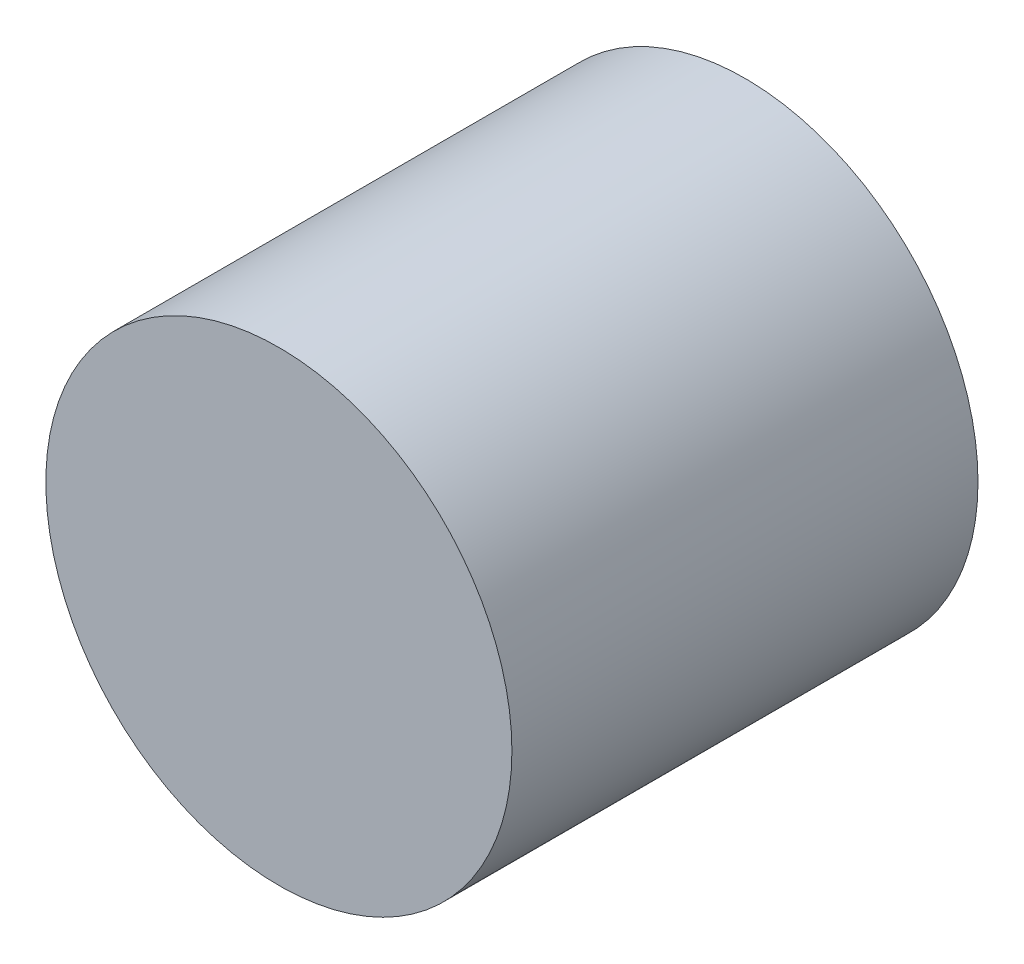
SolidWorks part; units mm, degrees
ref_plane "Front Plane" through (0, 0, 0) normal (0, 0, 1) x (1, 0, 0)
ref_plane "Top Plane" through (0, 0, 0) normal (0, 1, 0) x (1, 0, 0)
ref_plane "Right Plane" through (0, 0, 0) normal (1, 0, 0) x (0, 0, -1)
sketch "Sketch1" plane through (0, 0, 0) normal (0, 0, 1) x (1, 0, 0)
  circle A0 centre (2.6387, 20.8455) radius 20.32
extrude "Boss-Extrude2" add sketch "Sketch1" along normal blind 40.64
